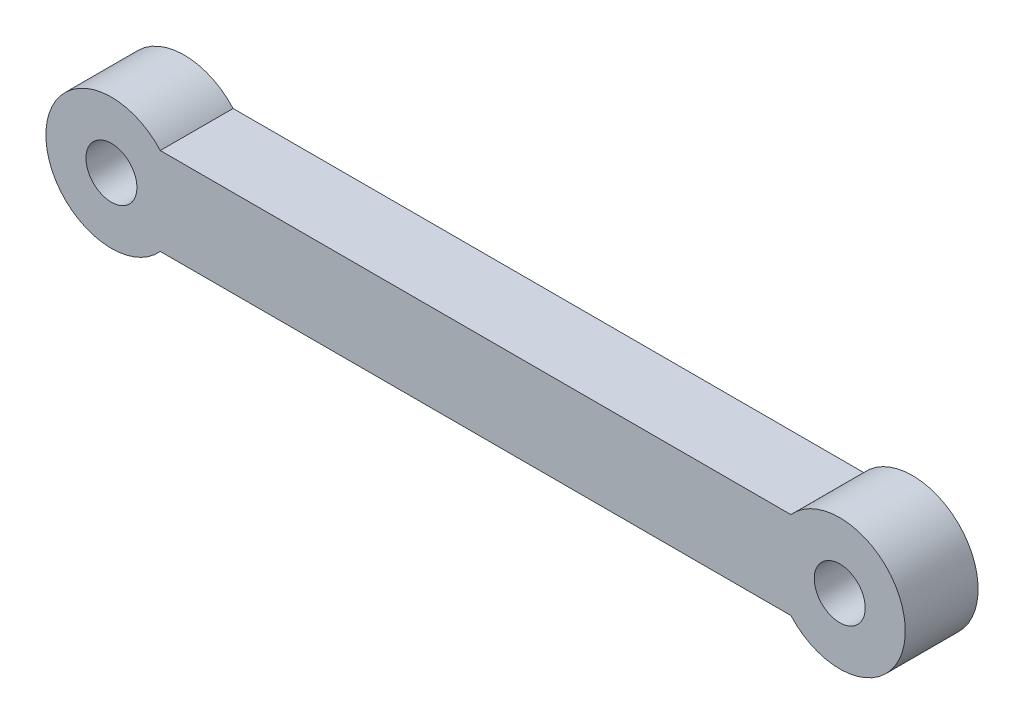
SolidWorks part; units mm, degrees
ref_plane "Plano frontal" through (0, 0, 0) normal (0, 0, 1) x (1, 0, 0)
ref_plane "Plano superior" through (0, 0, 0) normal (0, 1, 0) x (1, 0, 0)
ref_plane "Plano direito" through (0, 0, 0) normal (1, 0, 0) x (0, 0, -1)
sketch "Esboço1" plane through (0, 0, 0) normal (0, 0, 1) x (1, 0, 0)
  line L0 (-4.5, 0) -> (-45.5, 0) construction
  line L2 (-3.3541, 3) -> (-46.6459, 3)
  line L3 (-3.3541, -3) -> (-46.6459, -3)
  line L4 (-4.5, 3) -> (-45.5, 3) construction
  line L5 (-4.5, -3) -> (-45.5, -3) construction
  circle A0 centre (0, 0) radius 1.75
  arc A1 (-3.3541, -3) -> (-3.3541, 3) centre (0, 0) ccw
  circle A2 centre (-50, 0) radius 1.75
  arc A3 (-46.6459, 3) -> (-46.6459, -3) centre (-50, 0) ccw
  point P3 (0, 0)
  point P9 (-33.2437, 0)
  dimension "D1" = 9
  dimension "D2" = 3.5
  dimension "D3" = 9
  dimension "D4" = 3.5
  dimension "D5" = 50
  dimension "D6" = 3
  dimension "D7" = 3
extrude "Ressalto-extrusão1" add sketch "Esboço1" along normal blind 5
